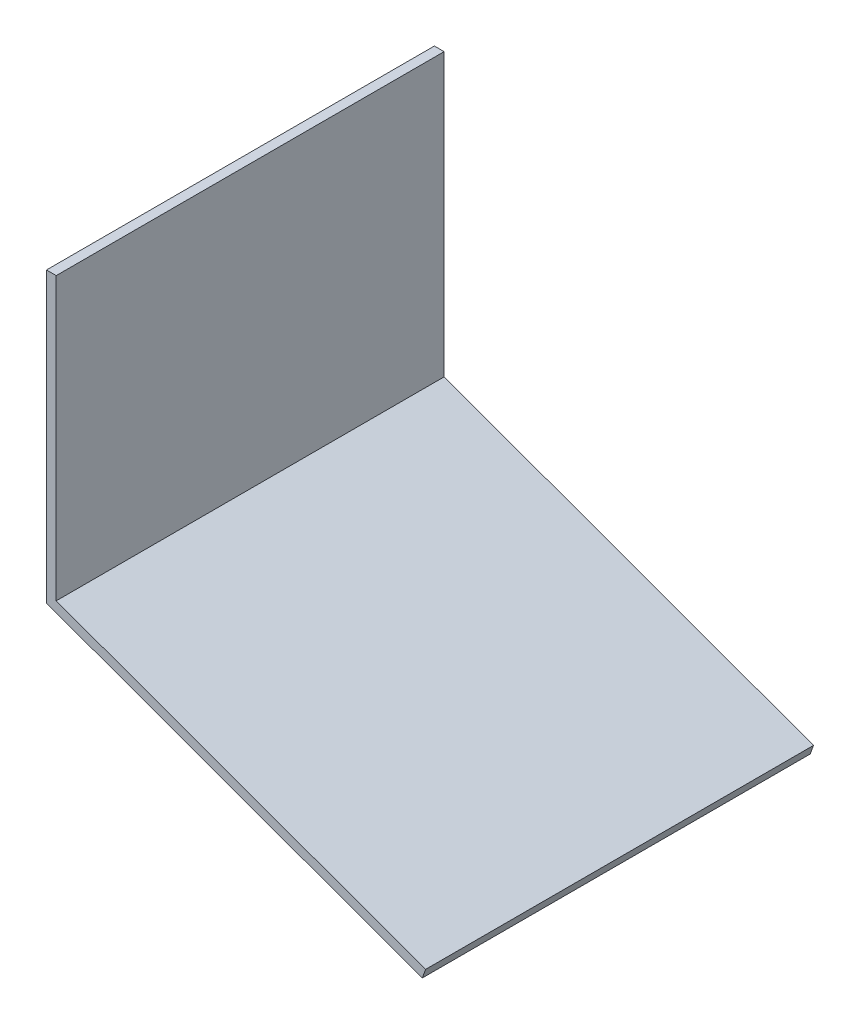
SolidWorks part; units mm, degrees
ref_plane "Front Plane" through (0, 0, 0) normal (0, 0, 1) x (1, 0, 0)
ref_plane "Top Plane" through (0, 0, 0) normal (0, 1, 0) x (1, 0, 0)
ref_plane "Right Plane" through (0, 0, 0) normal (1, 0, 0) x (0, 0, -1)
sketch "Sketch1" plane through (0, 0, 0) normal (0, 0, 1) x (1, 0, 0)
  line L0 (-22, 30) -> (-22, -114.5)
  line L1 (-22, -114.5) -> (167.5, -183.4724)
  line L2 (-22, -20) -> (-22, 470) construction
  line L3 (-22, -20) -> (-20, -20) construction
  line L4 (-27, 30) -> (-27, -118.001)
  line L5 (-27, -118.001) -> (165.7899, -188.1708)
  line L6 (-22, 30) -> (-27, 30)
  line L7 (167.5, -183.4724) -> (165.7899, -188.1708)
  line L8 (252.5, 470) -> (252.5, -20) construction
  line L9 (525, 470) -> (-20, 470) construction
  line L10 (-20, -20) -> (525, -20) construction
  line L11 (503.9, -114.5) -> (506.1, -114.5) construction
  point P18 (0, 0)
  point P19 (0, 0)
  point P22 (0, 0)
  dimension "D1" = 50
  dimension "D2" = 70
  dimension "D4" = 85
  dimension "D3" = 5
extrude "Boss-Extrude1" add sketch "Sketch1" against normal up to surface (199 mm away) from surface at 22
